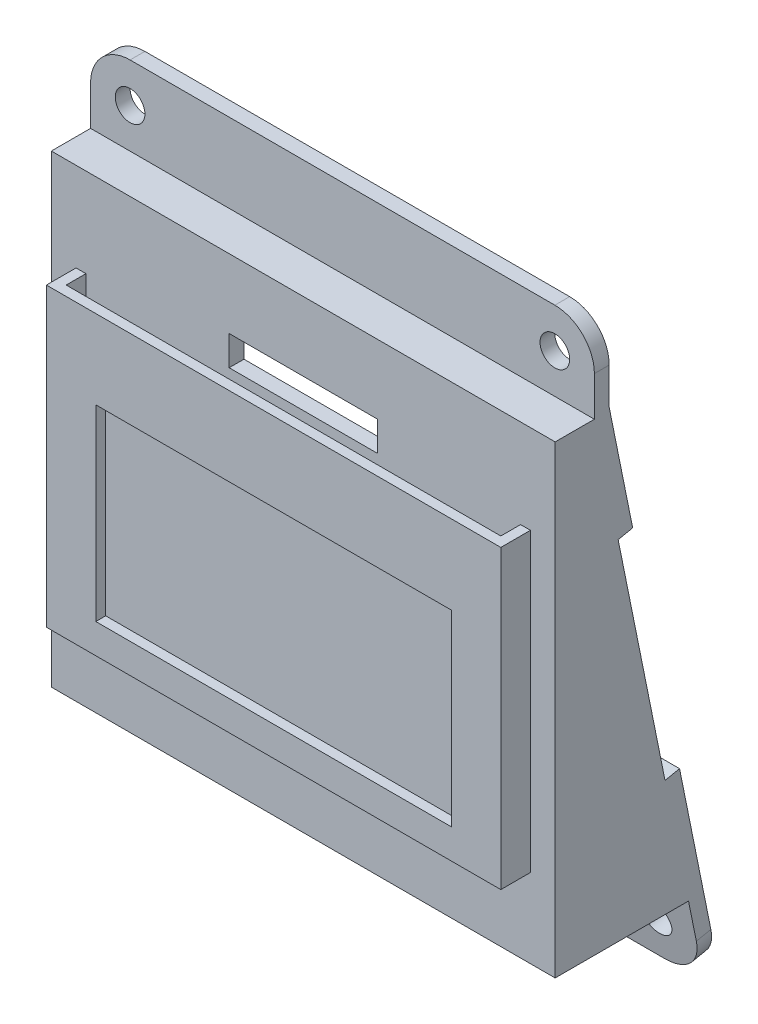
SolidWorks part; units mm, degrees
ref_plane "前视基准面" through (0, 0, 0) normal (0, 0, 1) x (1, 0, 0)
ref_plane "上视基准面" through (0, 0, 0) normal (0, 1, 0) x (1, 0, 0)
ref_plane "右视基准面" through (0, 0, 0) normal (1, 0, 0) x (0, 0, -1)
sketch "草图1" plane through (0, 0, 0) normal (0, 0, 1) x (1, 0, 0)
  line L0 (25.5, 47) -> (25.5, -10.5407) construction
  line L1 (0, 0) -> (51, 0)
  line L2 (0, 0) -> (0, 47)
  line L3 (0, 47) -> (51, 47)
  line L4 (51, 0) -> (51, 47)
  line L5 (18, 37) -> (33, 37)
  line L6 (33, 37) -> (33, 40)
  line L7 (33, 40) -> (18, 40)
  line L8 (18, 37) -> (18, 40)
  point P12 (25.5, 37)
  point P13 (25.5, 40)
  dimension "D1" = 51
  dimension "D2" = 47
  dimension "D3" = 37
  dimension "D4" = 3
  dimension "D5" = 15
extrude "凸台-拉伸1" add sketch "草图1" along normal blind 1.5
sketch "草图2" plane through (0, 0, 1.5) normal (0, 0, 1) x (1, 0, 0)
  line L0 (25.5, 8) -> (25.5, 47) construction
  line L1 (51, 47) -> (0, 47) construction
  line L2 (2.5, 8) -> (48.5, 8)
  line L3 (48.5, 8) -> (48.5, 38)
  line L4 (48.5, 38) -> (47.5, 38)
  line L5 (47.5, 38) -> (47.5, 9)
  line L6 (47.5, 9) -> (3.5, 9)
  line L7 (3.5, 38) -> (3.5, 9)
  line L8 (2.5, 38) -> (3.5, 38)
  line L9 (2.5, 8) -> (2.5, 38)
  line L10 (0, 0) -> (51, 0) construction
  point P10 (25.5, 9)
  point P13 (25.5, 47)
  dimension "D1" = 44
  dimension "D2" = 1
  dimension "D3" = 1
  dimension "D4" = 30
  dimension "D5" = 8
extrude "凸台-拉伸2" add sketch "草图2" along normal blind 2
sketch "草图3" plane through (0, 0, 3.5) normal (0, 0, 1) x (1, 0, 0)
  line L0 (25.5, 47) -> (25.5, -2.8361) construction
  line L1 (2.5, 8) -> (48.5, 8)
  line L2 (2.5, 8) -> (2.5, 38)
  line L3 (2.5, 38) -> (48.5, 38)
  line L4 (48.5, 8) -> (48.5, 38)
  line L5 (51, 47) -> (0, 47) construction
  line L6 (43.5, 30) -> (7.5, 30)
  line L7 (7.5, 30) -> (7.5, 11)
  line L8 (7.5, 11) -> (43.5, 11)
  line L9 (43.5, 30) -> (43.5, 11)
  line L10 (47.5, 9) -> (3.5, 9) construction
  point P15 (25.5, 11)
  point P16 (25.5, 30)
  point P18 (9.3681, 3.3617)
  dimension "D1" = 2
  dimension "D2" = 36
  dimension "D3" = 19
extrude "凸台-拉伸3" add sketch "草图3" along normal blind 1
sketch "草图4" plane through (0, 0, 0) normal (0, 0, -1) x (-1, 0, 0)
  line L1 (-51, 0) -> (0, 0)
  line L2 (-51, 0) -> (-51, 47)
  line L3 (-51, 47) -> (0, 47)
  line L4 (0, 0) -> (0, 47)
  line L5 (-49.5, 1.5) -> (-1.5, 1.5)
  line L6 (-49.5, 1.5) -> (-49.5, 46)
  line L7 (-49.5, 46) -> (-1.5, 46)
  line L8 (-1.5, 1.5) -> (-1.5, 46)
  dimension "D1" = 1.5
  dimension "D2" = 48
  dimension "D3" = 1.5
  dimension "D4" = 1
extrude "凸台-拉伸4" add sketch "草图4" along normal blind 12
sketch "草图5" plane through (51, 0, 0) normal (1, 0, 0) x (0, 0, -1)
  line L0 (2.5, 47) -> (12, 47)
  line L1 (-1.5, 47) -> (12, 47) construction
  line L2 (12, 47) -> (12, 0)
  line L3 (12, 0) -> (2.5, 47)
  line L4 (-1.5, 0) -> (-1.5, 47) construction
  dimension "D1" = 4
extrude "切除-拉伸1" cut sketch "草图5" against normal through all
sketch "草图6" plane through (0, 2.3303, -11.529) normal (0, 0.1981, -0.9802) x (-1, 0, 0)
  line L5 (-51, 45.573) -> (-51, -2.3775) construction
  line L6 (-51, 33.573) -> (0, 33.573)
  line L7 (-51, 33.573) -> (-51, 45.573)
  line L8 (-51, 45.573) -> (0, 45.573)
  line L9 (0, 33.573) -> (0, 45.573)
  line L10 (-51, -2.3775) -> (0, -2.3775) construction
  line L11 (-51, 9.6225) -> (0, 9.6225)
  line L12 (-51, 9.6225) -> (-51, -6.3775)
  line L13 (-47, -10.3775) -> (-4, -10.3775)
  line L14 (0, 9.6225) -> (0, -6.3775)
  line L15 (0, 45.573) -> (0, -2.3775) construction
  arc A0 (-4, -10.3775) -> (0, -6.3775) centre (-4, -6.3775) ccw
  arc A1 (-51, -6.3775) -> (-47, -10.3775) centre (-47, -6.3775) ccw
  circle A2 centre (-47, -6.3775) radius 1.5
  circle A3 centre (-4, -6.3775) radius 1.5
  point P16 (0, -10.3775)
  dimension "D4" = 4
  dimension "D5" = 3
  dimension "D6" = 3
  dimension "D1" = 8
  dimension "D2" = 20
  dimension "D3" = 12
extrude "凸台-拉伸5" add sketch "草图6" along normal blind 1.5
sketch "草图7" plane through (51, 0, 0) normal (1, 0, 0) x (0, 0, -1)
  line L0 (-1.5, 47) -> (2.5, 47) construction
  line L1 (2.4703, 47) -> (3.9703, 47)
  line L2 (2.4703, 47) -> (2.4703, 55)
  line L3 (2.4703, 55) -> (3.9703, 55)
  line L4 (3.9703, 47) -> (3.9703, 55)
  dimension "D1" = 1.5
  dimension "D2" = 8
extrude "凸台-拉伸6" add sketch "草图7" against normal blind 51
fillet "圆角1" radius 4 2 edges at (51, 55, -3.2203) (0, 55, -3.2203)
sketch "草图8" plane through (0, 0, -2.4703) normal (0, 0, 1) x (1, 0, 0)
  circle A0 centre (4, 51) radius 1.5
  circle A1 centre (47, 51) radius 1.5
  dimension "D1" = 3
  dimension "D2" = 3
extrude "切除-拉伸2" cut sketch "草图8" against normal up to next
sketch "草图9" plane through (0, 0, 0) normal (-1, 0, 0) x (0, 0, 1)
  line L0 (1.5, 0) -> (-12, 0) construction
  line L1 (1.5, 47) -> (1.5, 0) construction
  circle A0 centre (-4.5, 7) radius 4.5
  dimension "D1" = 9
  dimension "D2" = 7
  dimension "D3" = 6
extrude "切除-拉伸3" cut sketch "草图9" against normal up to next
